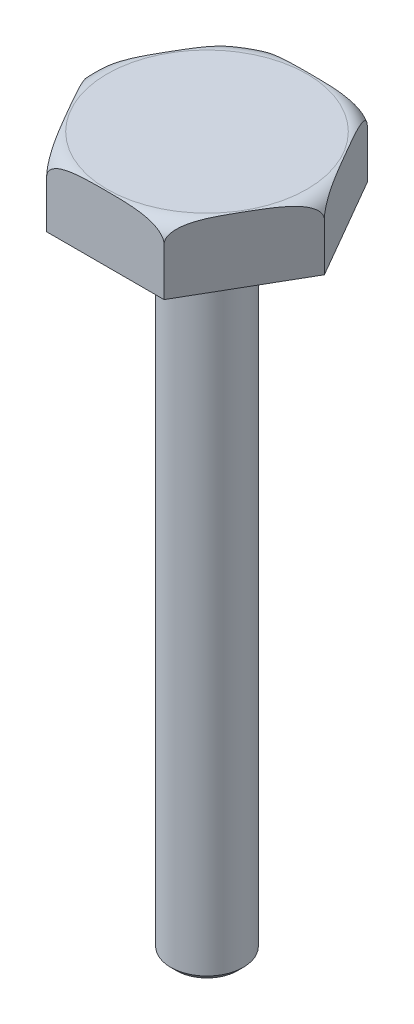
SolidWorks part; units mm, degrees
ref_plane "Front Plane" through (0, 0, 0) normal (0, 0, 1) x (1, 0, 0)
ref_plane "Top Plane" through (0, 0, 0) normal (0, 1, 0) x (1, 0, 0)
ref_plane "Right Plane" through (0, 0, 0) normal (1, 0, 0) x (0, 0, -1)
sketch "Sketch2" plane through (0, 0, 0) normal (0, 1, 0) x (1, 0, 0)
  line L1 (80.829, 0) -> (40.4145, 70)
  line L2 (40.4145, 70) -> (-40.4145, 70)
  line L3 (-40.4145, 70) -> (-80.829, 0)
  line L4 (-80.829, 0) -> (-40.4145, -70)
  line L5 (-40.4145, -70) -> (40.4145, -70)
  line L6 (40.4145, -70) -> (80.829, 0)
  circle A0 centre (0, 0) radius 70 construction
  point P1 (0, 0)
  dimension "D1" = 140
extrude "Boss-Extrude1" add sketch "Sketch2" along normal blind 45
sketch "Sketch3" plane through (0, 0, 0) normal (0, 1, 0) x (1, 0, 0)
  circle A0 centre (0, 0) radius 25
  dimension "D1" = 50
extrude "Boss-Extrude2" add sketch "Sketch3" against normal blind 445
sketch "Sketch4" plane through (0, 0, 0) normal (0, 0, 1) x (1, 0, 0)
  line L0 (80.829, 45) -> (80.829, 0) construction
  line L1 (40.4145, 45) -> (80.829, 45) construction
  line L2 (80.829, 33) -> (80.829, 45)
  line L3 (80.829, 45) -> (68.829, 45)
  line L4 (0, 0) -> (0, 9.7893) construction
  arc A0 (80.829, 33) -> (68.829, 45) centre (68.829, 33) ccw
  dimension "D1" = 12
revolve "Cut-Revolve1" cut sketch "Sketch4" angle 360 about L4
chamfer "Chamfer1" distance 4 angle 45 1 edges at (0, -445, 25)
